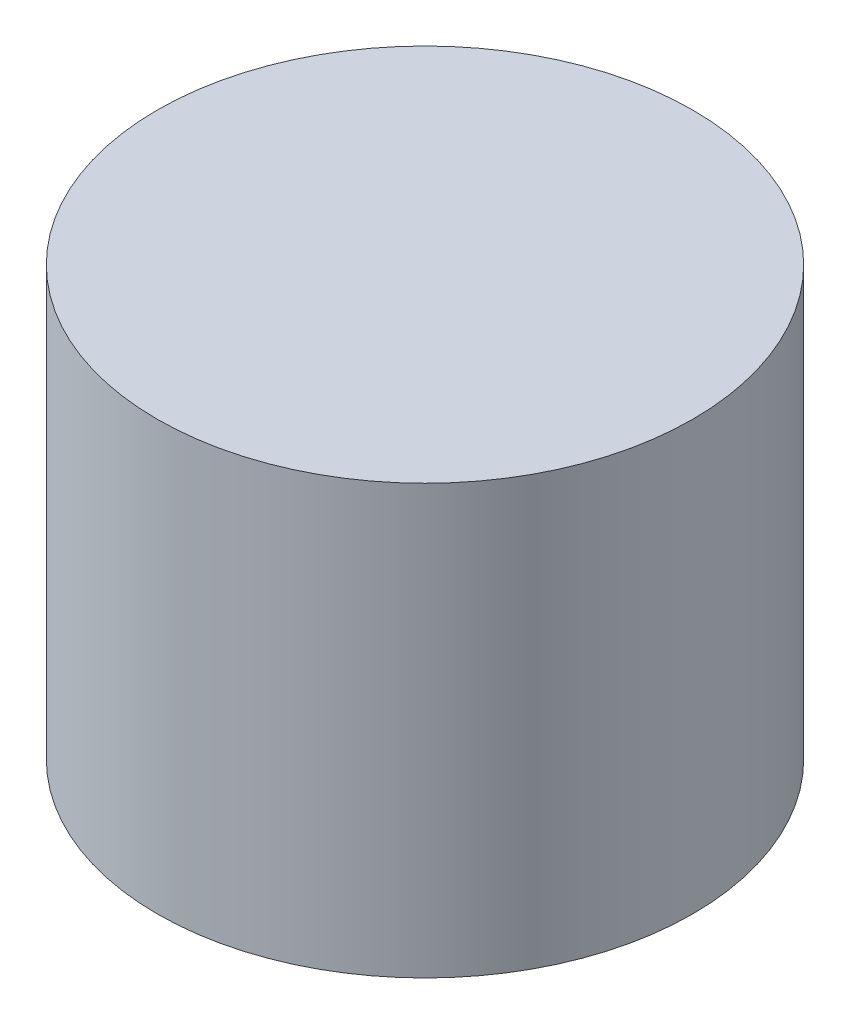
SolidWorks part; units mm, degrees
ref_plane "Front Plane" through (0, 0, 0) normal (0, 0, 1) x (1, 0, 0)
ref_plane "Top Plane" through (0, 0, 0) normal (0, 1, 0) x (1, 0, 0)
ref_plane "Right Plane" through (0, 0, 0) normal (1, 0, 0) x (0, 0, -1)
sketch "Sketch1" plane through (0, 0, 0) normal (0, 1, 0) x (1, 0, 0)
  circle A0 centre (0, 0) radius 12.5
  dimension "D1" = 25
extrude "Boss-Extrude1" add sketch "Sketch1" along normal blind 20
